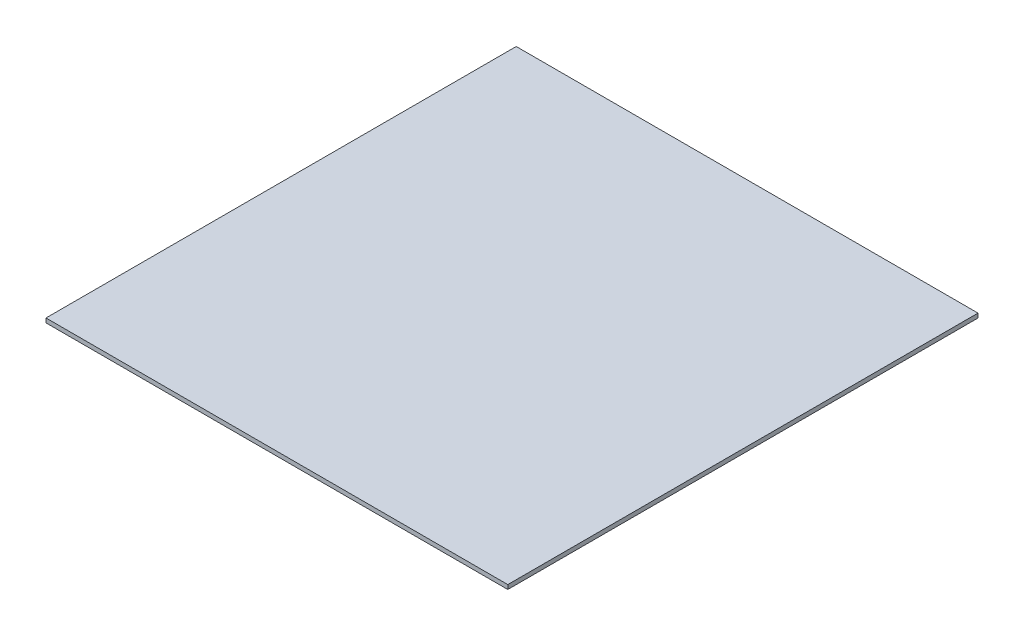
SolidWorks part; units mm, degrees
material "PVC Rigid"
ref_plane "Front Plane" through (0, 0, 0) normal (0, 0, 1) x (1, 0, 0)
ref_plane "Top Plane" through (0, 0, 0) normal (0, 1, 0) x (1, 0, 0)
ref_plane "Right Plane" through (0, 0, 0) normal (1, 0, 0) x (0, 0, -1)
sketch "Sketch1" plane through (0, 0, 0) normal (0, 1, 0) x (1, 0, 0)
  line L1 (0, -1390.4475) -> (2740, -1390.4475)
  line L2 (0, -1390.4475) -> (0, 1399.5525)
  line L3 (0, 1399.5525) -> (2740, 1399.5525)
  line L4 (2740, -1390.4475) -> (2740, 1399.5525)
  dimension "D1" = 2740
  dimension "D2" = 2790
extrude "Extrude1" add sketch "Sketch1" along normal blind 25.4
fillet "Fillet1" [suppressed] radius 254
sketch "Sketch2" plane through (0, 0, 0) normal (0, -1, 0) x (1, 0, 0)
  line L0 (0, -1051.6337) -> (2740, -1051.6337)
  line L1 (0, -1399.5525) -> (0, 1390.4475) construction
  line L2 (2740, 1390.4475) -> (2740, -1399.5525) construction
split line "Split Line1" [suppressed]
sketch "Sketch3" [suppressed] plane through (0, 0, 0) normal (0, -1, 0) x (1, 0, 0)
  line L0 (0, -871.6337) -> (2000, -871.6337)
  line L1 (0, -1051.6337) -> (0, -254) construction
  line L2 (2000, -254) -> (2000, -1051.6337) construction
  line L3 (2000, -1051.6337) -> (0, -1051.6337) construction
  dimension "D1" = 180
split line "Split Line2" [suppressed]
